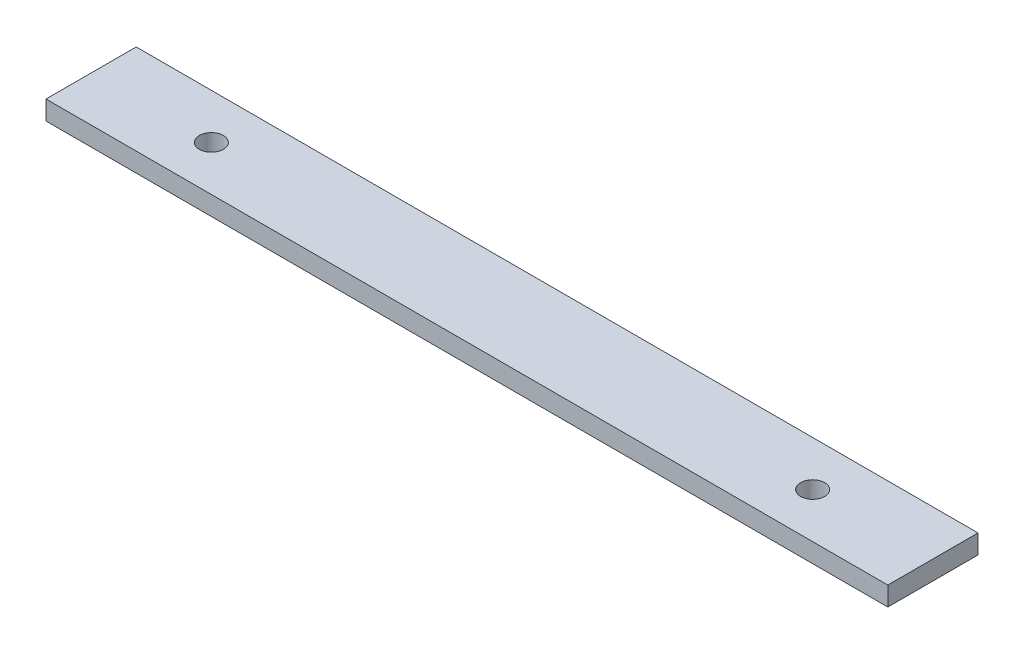
SolidWorks part; units mm, degrees
ref_plane "Front Plane" through (0, 0, 0) normal (0, 0, 1) x (1, 0, 0)
ref_plane "Top Plane" through (0, 0, 0) normal (0, 1, 0) x (1, 0, 0)
ref_plane "Right Plane" through (0, 0, 0) normal (1, 0, 0) x (0, 0, -1)
sketch "Sketch1" plane through (0, 0, 0) normal (0, 1, 0) x (1, 0, 0)
  line L0 (50, 0) -> (-50, 0) construction
  line L1 (70, 7.5) -> (-70, 7.5)
  line L2 (70, 7.5) -> (70, -7.5)
  line L3 (70, -7.5) -> (-70, -7.5)
  line L4 (-70, 7.5) -> (-70, -7.5)
  line L5 (70, 7.5) -> (-70, -7.5) construction
  line L6 (70, -7.5) -> (-70, 7.5) construction
  circle A0 centre (-50, 0) radius 2
  circle A1 centre (50, 0) radius 2
  point P0 (0, 0)
  point P9 (0, 0)
  dimension "D4" = 4
  dimension "D1" = 15
  dimension "D2" = 140
  dimension "D3" = 100
extrude "Boss-Extrude1" add sketch "Sketch1" along normal blind 3.175
